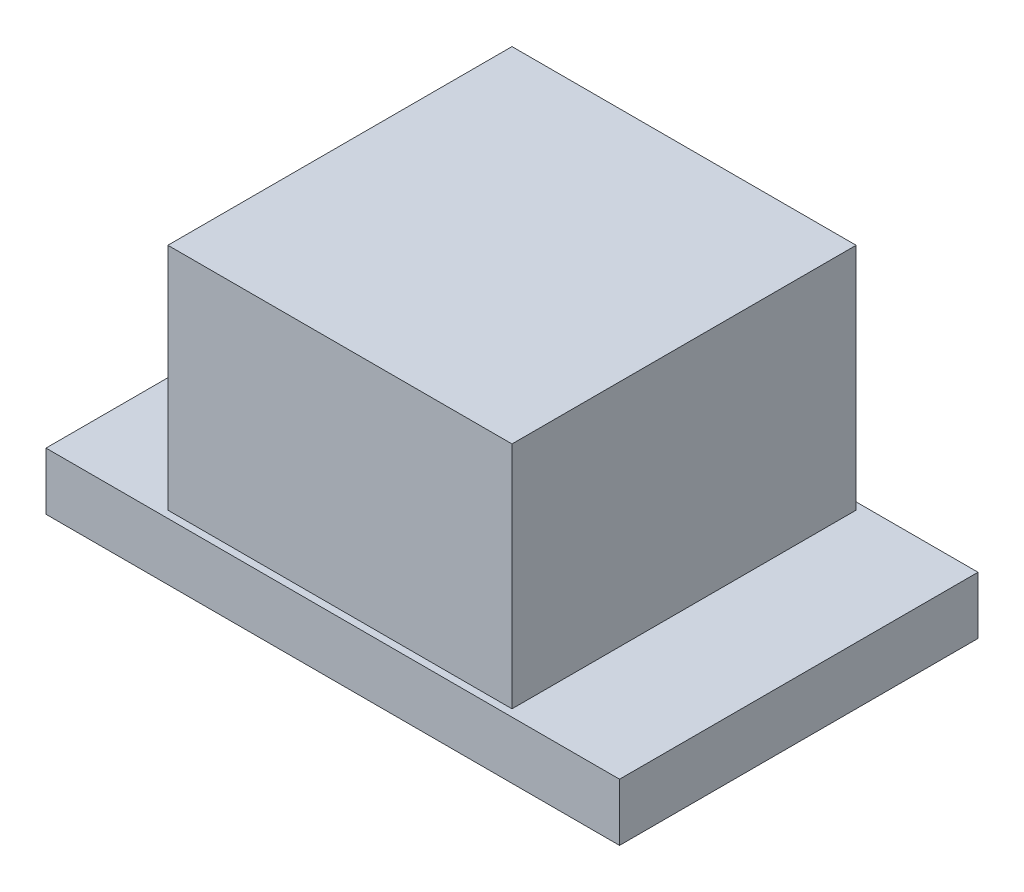
SolidWorks part; units mm, degrees
ref_plane "Front Plane" through (0, 0, 0) normal (0, 0, 1) x (1, 0, 0)
ref_plane "Top Plane" through (0, 0, 0) normal (0, 1, 0) x (1, 0, 0)
ref_plane "Right Plane" through (0, 0, 0) normal (1, 0, 0) x (0, 0, -1)
sketch "Sketch1" plane through (0, 0, 0) normal (0, 1, 0) x (1, 0, 0)
  circle A0 centre (0, 0) radius 0.1
  dimension "D1" = 0.2
extrude "Boss-Extrude1" add sketch "Sketch1" along normal blind 0.3
sketch "Sketch2" plane through (0, 0, 0) normal (0, 1, 0) x (1, 0, 0)
  line L1 (-1, 0.625) -> (1, 0.625)
  line L2 (-1, 0.625) -> (-1, -0.625)
  line L3 (-1, -0.625) -> (1, -0.625)
  line L4 (1, 0.625) -> (1, -0.625)
  line L5 (-1, 0.625) -> (1, -0.625) construction
  line L6 (-1, -0.625) -> (1, 0.625) construction
  point P0 (0, 0)
  dimension "D1" = 2
  dimension "D2" = 1.25
extrude "Boss-Extrude2" add sketch "Sketch2" along normal blind 0.2
sketch "Sketch3" plane through (0, 0.2, 0) normal (0, 1, 0) x (1, 0, 0)
  line L1 (-0.6, 0.6) -> (0.6, 0.6)
  line L2 (-0.6, 0.6) -> (-0.6, -0.6)
  line L3 (-0.6, -0.6) -> (0.6, -0.6)
  line L4 (0.6, 0.6) -> (0.6, -0.6)
  line L5 (-0.6, 0.6) -> (0.6, -0.6) construction
  line L6 (-0.6, -0.6) -> (0.6, 0.6) construction
  point P0 (0, 0)
  dimension "D1" = 1.2
  dimension "D2" = 1.2
extrude "Cut-Extrude1" cut sketch "Sketch3" against normal blind 0.01
sketch "Sketch4" plane through (0, 0.19, 0) normal (0, 1, 0) x (1, 0, 0)
  line L4 (0.6, -0.6) -> (0.6, 0.6)
  line L5 (0.6, 0.6) -> (-0.6, 0.6)
  line L6 (-0.6, 0.6) -> (-0.6, -0.6)
  line L7 (-0.6, -0.6) -> (0.6, -0.6)
  line L8 (0.6, -0.6) -> (0.6, 0.6)
  line L9 (0.6, 0.6) -> (-0.6, 0.6)
  line L10 (-0.6, 0.6) -> (-0.6, -0.6)
  line L11 (-0.6, -0.6) -> (0.6, -0.6)
  dimension "D1" = 0
extrude "Boss-Extrude4" add sketch "Sketch4" along normal blind 0.01 separate body
sketch "Sketch5" plane through (0, 0.2, 0) normal (0, 1, 0) x (1, 0, 0)
  line L4 (-0.6, -0.6) -> (0.6, -0.6)
  line L5 (0.6, -0.6) -> (0.6, 0.6)
  line L6 (0.6, 0.6) -> (-0.6, 0.6)
  line L7 (-0.6, 0.6) -> (-0.6, -0.6)
  line L8 (-0.6, -0.6) -> (0.6, -0.6)
  line L9 (0.6, -0.6) -> (0.6, 0.6)
  line L10 (0.6, 0.6) -> (-0.6, 0.6)
  line L11 (-0.6, 0.6) -> (-0.6, -0.6)
  dimension "D1" = 0
extrude "Boss-Extrude5" add sketch "Sketch5" along normal blind 0.8 separate body
